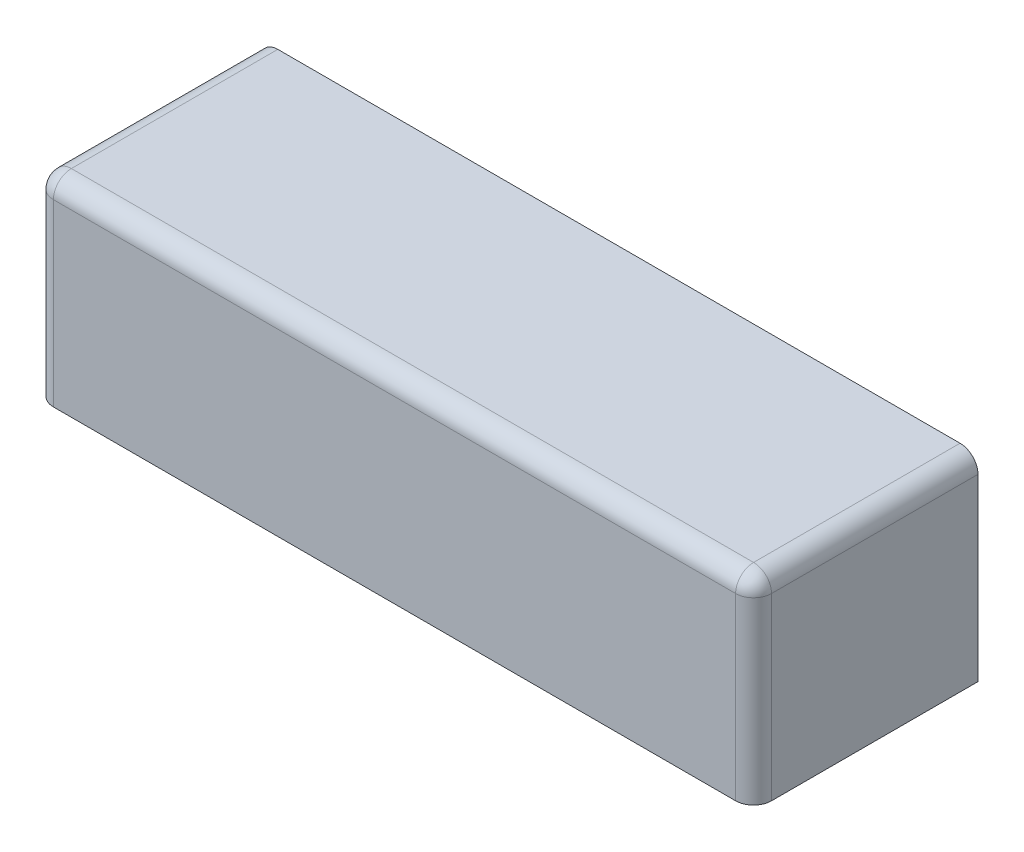
SolidWorks part; units mm, degrees
material "聚亚安酯(11671)"
ref_plane "前视基准面" through (0, 0, 0) normal (0, 0, 1) x (1, 0, 0)
ref_plane "上视基准面" through (0, 0, 0) normal (0, 1, 0) x (1, 0, 0)
ref_plane "右视基准面" through (0, 0, 0) normal (1, 0, 0) x (0, 0, -1)
sketch "草图1" plane through (0, 0, 0) normal (0, 0, 1) x (1, 0, 0)
  line L1 (-200, 55) -> (200, 55)
  line L2 (-200, 55) -> (-200, -55)
  line L3 (-200, -55) -> (200, -55)
  line L4 (200, 55) -> (200, -55)
  line L5 (-200, 55) -> (200, -55) construction
  line L6 (-200, -55) -> (200, 55) construction
  point P0 (0, 0)
  dimension "D1" = 400
  dimension "D2" = 110
extrude "凸台-拉伸1" add sketch "草图1" along normal blind 125
fillet "圆角1" radius 10 5 edges at (-200, 55, 62.5) (-200, 0, 125) (200, 0, 125) (200, 55, 62.5) (0, 55, 125)
shell "抽壳1" thickness 3
